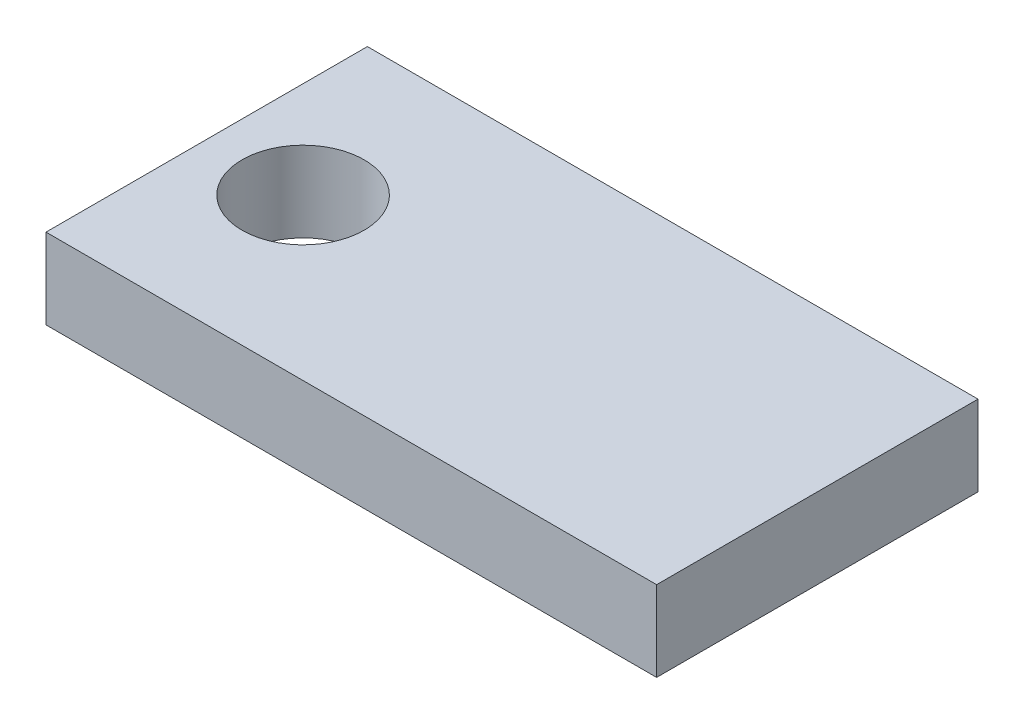
SolidWorks part; units mm, degrees
material "6061 Alloy"
ref_plane "Front Plane" through (0, 0, 0) normal (0, 0, 1) x (1, 0, 0)
ref_plane "Top Plane" through (0, 0, 0) normal (0, 1, 0) x (1, 0, 0)
ref_plane "Right Plane" through (0, 0, 0) normal (1, 0, 0) x (0, 0, -1)
sketch "Sketch1" plane through (0, 0, 0) normal (0, 1, 0) x (1, 0, 0)
  line L1 (24.13, -12.7) -> (-24.13, -12.7)
  line L2 (24.13, -12.7) -> (24.13, 12.7)
  line L3 (24.13, 12.7) -> (-24.13, 12.7)
  line L4 (-24.13, -12.7) -> (-24.13, 12.7)
  line L5 (24.13, -12.7) -> (-24.13, 12.7) construction
  line L6 (24.13, 12.7) -> (-24.13, -12.7) construction
  point P0 (0, 0)
  dimension "D1" = 48.26
  dimension "D2" = 25.4
extrude "Boss-Extrude1" add sketch "Sketch1" along normal blind 6.35
sketch "Sketch2" plane through (0, 6.35, 0) normal (0, 1, 0) x (1, 0, 0)
  line L0 (-24.13, 12.7) -> (-24.13, -12.7) construction
  line L1 (-24.13, -12.7) -> (24.13, -12.7) construction
  circle A0 centre (-16.51, 0) radius 4.826
  dimension "D1" = 9.652
  dimension "D2" = 7.62
  dimension "D3" = 12.7
extrude "Cut-Extrude1" cut sketch "Sketch2" against normal blind 8.89
